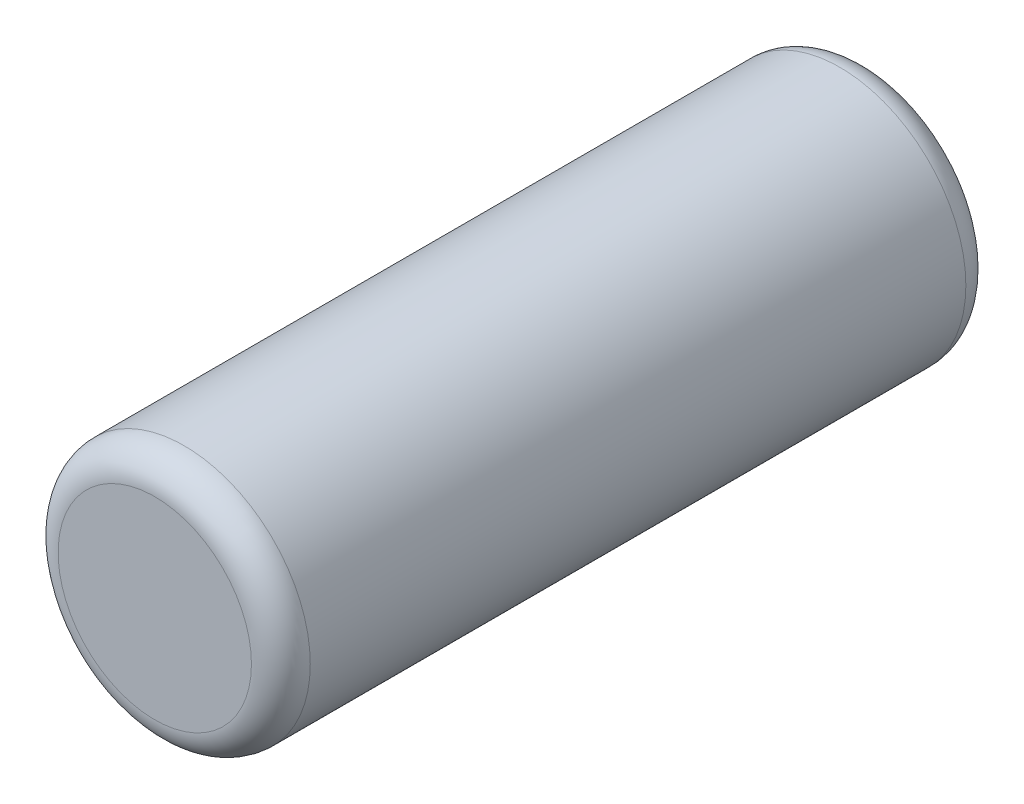
SolidWorks part; units mm, degrees
ref_plane "Front" through (0, 0, 0) normal (0, 0, 1) x (1, 0, 0)
ref_plane "Top" through (0, 0, 0) normal (0, 1, 0) x (1, 0, 0)
ref_plane "Right" through (0, 0, 0) normal (1, 0, 0) x (0, 0, -1)
sketch "Sketch1" plane through (0, 0, 0) normal (0, 0, 1) x (1, 0, 0)
  circle A0 centre (0, 0) radius 1.5
  dimension "D1" = 3
extrude "Boss-Extrude1" add sketch "Sketch1" along normal mid plane 8.5
fillet "Fillet1" radius 0.35 2 edges at (1.5, 0, -4.25) (1.5, 0, 4.25)
